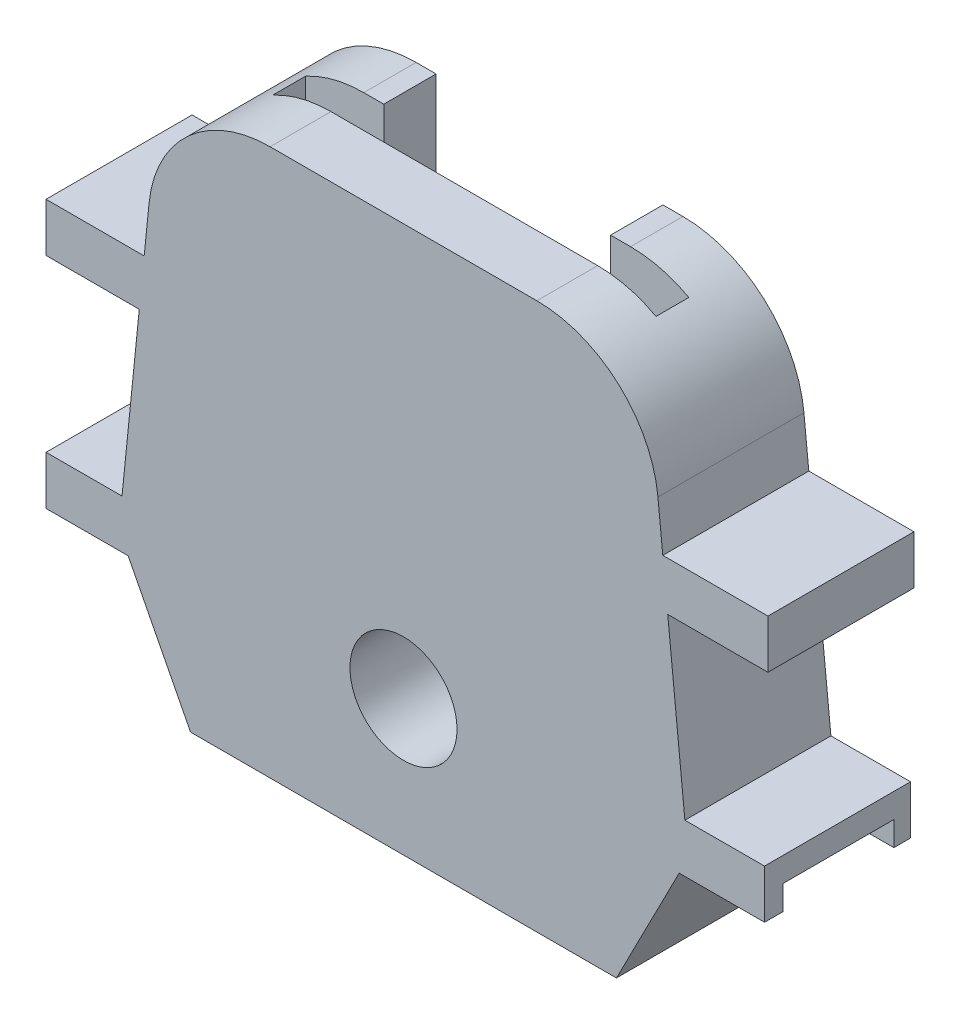
SolidWorks part; units mm, degrees
ref_plane "Front Plane" through (0, 0, 0) normal (0, 0, 1) x (1, 0, 0)
ref_plane "Top Plane" through (0, 0, 0) normal (0, 1, 0) x (1, 0, 0)
ref_plane "Right Plane" through (0, 0, 0) normal (1, 0, 0) x (0, 0, -1)
sketch "Sketch2" plane through (0, 0, 0) normal (0, 0, 1) x (1, 0, 0)
  line L0 (-26.6527, 24.7995) -> (-27.0526, 20.8472)
  line L1 (-16.7035, 33.7929) -> (5.2179, 33.7929)
  line L3 (-23.2428, -11.1376) -> (11.7572, -11.1376)
  line L5 (-28.3709, -1.1522) -> (-23.2428, -11.1376)
  line L6 (15.1671, 24.7995) -> (15.567, 20.8472)
  line L7 (16.9145, -1.095) -> (11.7572, -11.1376)
  line L8 (-5.7428, 33.7929) -> (-5.7428, -11.1376) construction
  line L14 (-28.8738, 2.8472) -> (-28.8738, 20.8472) construction
  line L16 (-28.8738, 2.8472) -> (-35.118, 2.8393)
  line L17 (23.9316, -1.0861) -> (16.9145, -1.095)
  line L18 (23.9316, -1.0861) -> (23.9266, 2.9139)
  line L19 (-35.1129, -1.1607) -> (-35.118, 2.8393)
  line L20 (23.9266, 2.9139) -> (17.3823, 2.9056)
  line L21 (-1028.8738, 20.8472) -> (-27.0526, 20.8472) construction
  line L22 (-35.118, 2.8393) -> (-35.118, 30.8551) construction
  line L23 (-27.4573, 16.8472) -> (-28.8738, 2.8472)
  line L25 (-28.3709, -1.1522) -> (-35.1129, -1.1607)
  line L26 (-35.118, 16.8472) -> (-27.4573, 16.8472)
  line L27 (-35.118, 16.8472) -> (-35.118, 20.8472)
  line L28 (-35.118, 20.8472) -> (-27.0526, 20.8472)
  line L29 (24.2077, 16.8472) -> (24.2077, 20.8472)
  line L30 (15.9717, 16.8472) -> (17.3823, 2.9056)
  line L31 (15.567, 20.8472) -> (1002.5829, 20.8472) construction
  line L32 (15.567, 20.8472) -> (24.2077, 20.8472)
  line L33 (15.9717, 16.8472) -> (24.2077, 16.8472)
  circle A0 centre (-5.7428, 0) radius 4.4
  arc A1 (15.1671, 24.7995) -> (5.2179, 33.7929) centre (5.2179, 23.7929) ccw
  arc A2 (-16.7035, 33.7929) -> (-26.6527, 24.7995) centre (-16.7035, 23.7929) ccw
  point P31 (14.2572, 33.7929)
  point P34 (-25.7428, 33.7929)
  dimension "D3" = 8.8
  dimension "D7" = 10
  dimension "D1" = 35
  dimension "D2" = 4
  dimension "D4" = 40
  dimension "D5" = 4
  dimension "D6" = 18
extrude "Boss-Extrude1" add sketch "Sketch2" along normal blind 12
sketch "Sketch3" plane through (0.0014, -1.1163, 0) normal (0.0013, -1, 0) x (1, 0.0013, 0)
  line L0 (-35.1144, 12) -> (-35.1144, 0) construction
  line L1 (-35.1144, 10.5) -> (-29.1144, 10.5)
  line L2 (-35.1144, 10.5) -> (-35.1144, 8.5)
  line L4 (-29.1144, 10.5) -> (-29.1144, 8.5)
  line L10 (-35.1144, 3.5238) -> (-35.1144, 1.4619)
  line L11 (-35.1144, 1.4619) -> (-29.1144, 1.4619)
  line L12 (-29.1144, 3.5238) -> (-29.1144, 1.4619)
  line L13 (17.9302, 10.5) -> (23.9302, 10.5)
  line L14 (17.9302, 10.5) -> (17.9302, 8.5)
  line L16 (23.9302, 10.5) -> (23.9302, 8.5)
  line L22 (17.9302, 3.4381) -> (17.9302, 1.3762)
  line L23 (17.9302, 1.3762) -> (23.9302, 1.3762)
  line L24 (23.9302, 3.4381) -> (23.9302, 1.3762)
  line L25 (23.9302, 12) -> (23.9302, 0) construction
  line L26 (-35.1144, 12) -> (-28.3724, 12) construction
  line L27 (16.9131, 12) -> (23.9302, 12) construction
  line L28 (-35.1144, 8.5) -> (-35.1144, 3.5238)
  line L29 (-29.1144, 3.5238) -> (-29.1144, 8.5)
  line L31 (23.9302, 3.4381) -> (23.9302, 8.5)
  line L32 (17.9302, 8.5) -> (17.9302, 3.4381)
  dimension "D1" = 6
  dimension "D3" = 1.5
  dimension "D6" = 6
  dimension "D8" = 1.5
extrude "Cut-Extrude1" cut sketch "Sketch3" against normal blind 2
ref_plane "Plane1" through (0, 0, 7) normal (0, 0, 1) x (1, 0, 0)
sketch "Sketch4" plane through (0, 0, 7) normal (0, 0, 1) x (1, 0, 0)
  line L0 (-5.7428, 33.7929) -> (-5.7428, -11.1376) construction
  line L1 (5.2179, 33.7929) -> (-16.7035, 33.7929) construction
  line L2 (-23.2428, -11.1376) -> (11.7572, -11.1376) construction
  line L3 (-21.4928, 33.7929) -> (10.0072, 33.7929)
  line L4 (-21.4928, 33.7929) -> (-21.4928, 7.2929)
  line L5 (10.0072, 33.7929) -> (10.0072, 7.2929)
  line L6 (-21.4928, 7.2929) -> (10.0072, 7.2929)
  line L7 (-21.4928, 33.7929) -> (10.0072, 7.2929) construction
  line L8 (10.0072, 33.7929) -> (-21.4928, 7.2929) construction
  point P7 (-5.7428, 20.5429)
  dimension "D1" = 26.5
  dimension "D2" = 31.5
extrude "Cut-Extrude2" cut sketch "Sketch4" against normal blind 2.7
sketch "Sketch5" plane through (0, 0, 0) normal (0, 0, -1) x (-1, 0, 0)
  line L0 (5.7428, 33.7929) -> (5.7428, -11.1376) construction
  line L1 (-5.2179, 33.7929) -> (16.7035, 33.7929) construction
  line L2 (23.2428, -11.1376) -> (-11.7572, -11.1376) construction
  line L4 (-3.5775, 8.7929) -> (15.0631, 8.7929)
  line L5 (-3.5775, 8.7929) -> (-3.5775, 33.7929)
  line L6 (-3.5775, 33.7929) -> (15.0631, 33.7929)
  line L7 (15.0631, 8.7929) -> (15.0631, 33.7929)
  line L8 (-3.5775, 8.7929) -> (15.0631, 33.7929) construction
  line L9 (-3.5775, 33.7929) -> (15.0631, 8.7929) construction
  point P6 (5.7428, 21.2929)
  dimension "D1" = 25
extrude "Cut-Extrude3" cut sketch "Sketch5" against normal up to next
